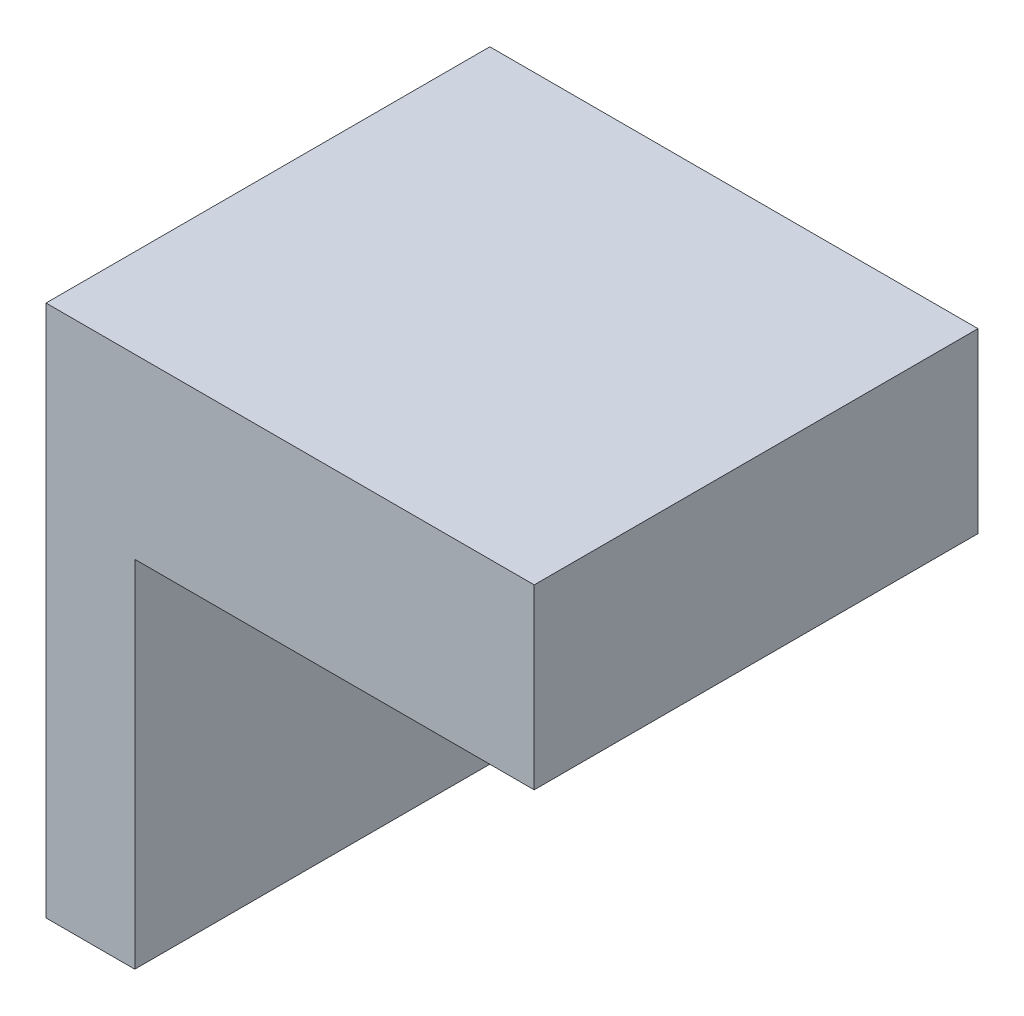
SolidWorks part; units mm, degrees
ref_plane "Alzado" through (0, 0, 0) normal (0, 0, 1) x (1, 0, 0)
ref_plane "Planta" through (0, 0, 0) normal (0, 1, 0) x (1, 0, 0)
ref_plane "Vista lateral" through (0, 0, 0) normal (1, 0, 0) x (0, 0, -1)
sketch "Croquis1" plane through (0, 0, 0) normal (0, 0, 1) x (1, 0, 0)
  line L0 (-42.313, -15.1463) -> (12.687, -15.1463)
  line L1 (-42.313, -15.1463) -> (-42.313, -75.1463)
  line L2 (-42.313, -75.1463) -> (-32.313, -75.1463)
  line L3 (-32.313, -75.1463) -> (-32.313, -35.1463)
  line L4 (-32.313, -35.1463) -> (12.687, -35.1463)
  line L5 (12.687, -35.1463) -> (12.687, -15.1463)
extrude "Saliente-Extruir1" add sketch "Croquis1" along normal blind 50
hole_wizard "Perforador para roscar para macho de roscar para M6x1.01" positions "Croquis3D1" profile "Croquis2" hole size "M6x1.0" standard "Ansi Metric"
sketch3d "Croquis3D1"
  line L0 (-32.313, -75.1463, 0) -> (-32.313, -35.1463, 0) construction
  line L1 (-32.313, -75.1463, 50) -> (-32.313, -75.1463, 0) construction
  point P0 (-32.313, -55.1463, 25)
  dimension "D1" = 25
  dimension "D2" = 20
sketch "Croquis2" plane through (-32.313, -55.1463, 25) normal (0, 1, 0) x (0, 0, -1)
  line L0 (0, 0) -> (0, 12.5022)
  line L1 (0, 12.5022) -> (2.5, 11)
  line L2 (2.5, 11) -> (2.5, 0)
  line L5 (2.5, 0) -> (0, 0)
  line L10 (0, 12.5022) -> (-2.5, 11) construction
  line L11 (0, -6.35) -> (0, 107.95) construction
  dimension "Diámetro de taladro" = 5
  dimension "Profundidad de taladro" = 11
  dimension "Ángulo de perforador" = 118
